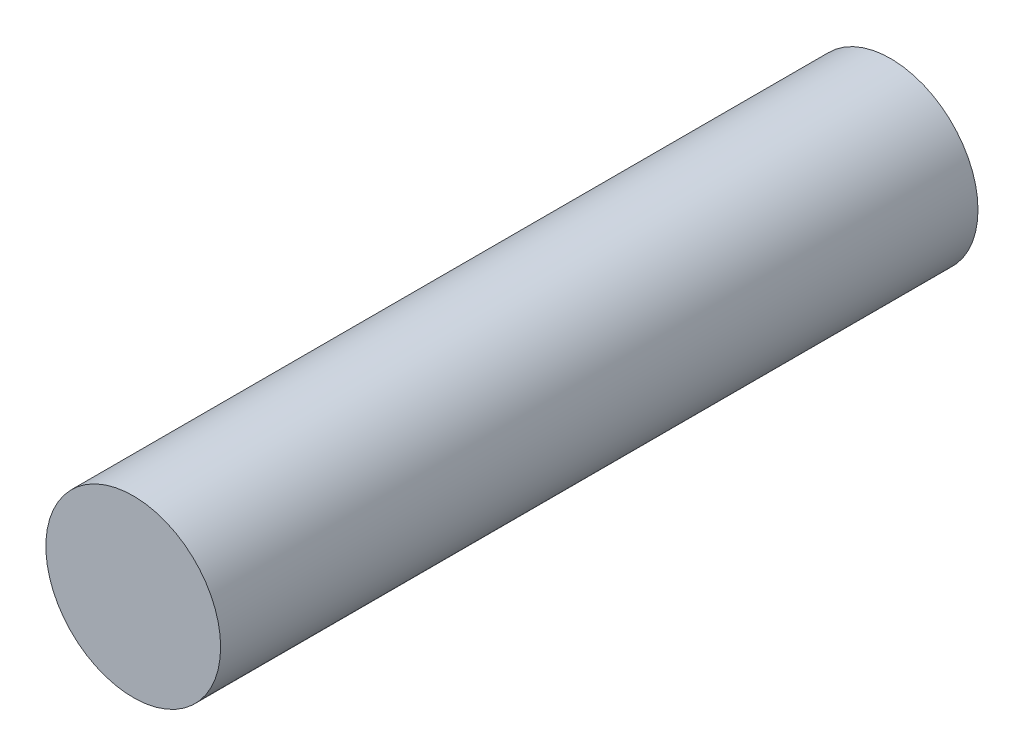
SolidWorks part; units mm, degrees
material "AISI 304"
ref_plane "Front Plane" through (0, 0, 0) normal (0, 0, 1) x (1, 0, 0)
ref_plane "Top Plane" through (0, 0, 0) normal (0, 1, 0) x (1, 0, 0)
ref_plane "Right Plane" through (0, 0, 0) normal (1, 0, 0) x (0, 0, -1)
sketch "Sketch1" plane through (0, 0, 0) normal (0, 0, 1) x (1, 0, 0)
  circle A0 centre (0, 0) radius 3
  dimension "D1" = 6
extrude "Boss-Extrude1" add sketch "Sketch1" along normal blind 26
